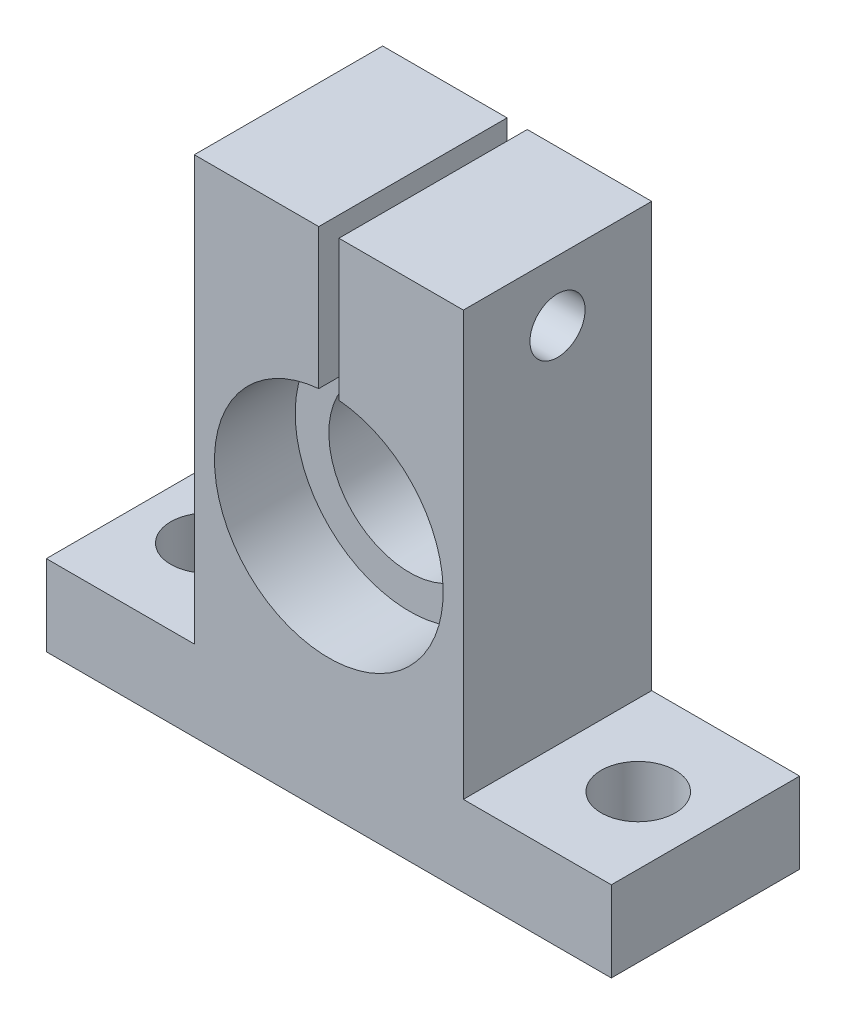
SolidWorks part; units mm, degrees
ref_plane "Front Plane" through (0, 0, 0) normal (0, 0, 1) x (1, 0, 0)
ref_plane "Top Plane" through (0, 0, 0) normal (0, 1, 0) x (1, 0, 0)
ref_plane "Right Plane" through (0, 0, 0) normal (1, 0, 0) x (0, 0, -1)
sketch "Sketch1" plane through (0, 0, 0) normal (0, 0, 1) x (1, 0, 0)
  line L0 (0, 0) -> (21, 0)
  line L1 (21, 0) -> (21, 6)
  line L2 (21, 6) -> (10, 6)
  line L3 (10, 6) -> (10, 37.5)
  line L4 (10, 37.5) -> (0, 37.5)
  line L5 (0, 37.5) -> (0, 0)
  line L9 (0, -1000) -> (0, 49000) construction
  dimension "D1" = 37.5
  dimension "D2" = 6
  dimension "D3" = 21
  dimension "D4" = 10
extrude "Boss-Extrude1" add sketch "Sketch1" along normal mid plane 14
mirror "Mirror1" about plane through (0, 37.5, 7) normal (1, 0, 0) of "Boss-Extrude1"
sketch "Sketch2" plane through (0, 0, 7) normal (0, 0, 1) x (1, 0, 0)
  circle A0 centre (0, 18.6) radius 6
  dimension "D1" = 12
  dimension "D2" = 18.6
extrude "Cut-Extrude1" cut sketch "Sketch2" against normal through all
sketch "Sketch3" plane through (10, 0, 0) normal (1, 0, 0) x (0, 0, -1)
  line L1 (-7, 37.5) -> (7, 37.5) construction
  circle A0 centre (0, 33) radius 2.05
  dimension "D2" = 4.1
  dimension "D1" = 4.5
extrude "Cut-Extrude2" cut sketch "Sketch3" against normal through all
sketch "Sketch4" plane through (0, 6, 0) normal (0, 1, 0) x (1, 0, 0)
  circle A0 centre (-16, 0) radius 2.75
  circle A1 centre (16, 0) radius 2.75
  dimension "D2" = 5.5
  dimension "D3" = 5.5
  dimension "D1" = 16
  dimension "D4" = 16
extrude "Cut-Extrude3" cut sketch "Sketch4" against normal blind 14
sketch "Sketch5" plane through (0, 0, 7) normal (0, 0, 1) x (1, 0, 0)
  line L0 (-0.75, 52) -> (-0.75, 23)
  line L1 (-0.75, 52) -> (0.75, 52)
  line L2 (-0.75, 23) -> (0.75, 23)
  line L3 (0.75, 52) -> (0.75, 23)
  line L4 (-0.75, 52) -> (0.75, 23) construction
  line L5 (-0.75, 23) -> (0.75, 52) construction
  line L7 (10, 37.5) -> (-10, 37.5) construction
  point P1 (0, 37.5)
  dimension "D1" = 1.5
  dimension "D2" = 90
extrude "Cut-Extrude4" cut sketch "Sketch5" against normal through all
sketch "Sketch6" plane through (0, 0, 7) normal (0, 0, 1) x (1, 0, 0)
  circle A0 centre (0, 18.6) radius 8.5
  dimension "D1" = 17
extrude "Cut-Extrude5" cut sketch "Sketch6" against normal blind 6
equation "\"D2@Sketch2\"=23.00-4.4"
